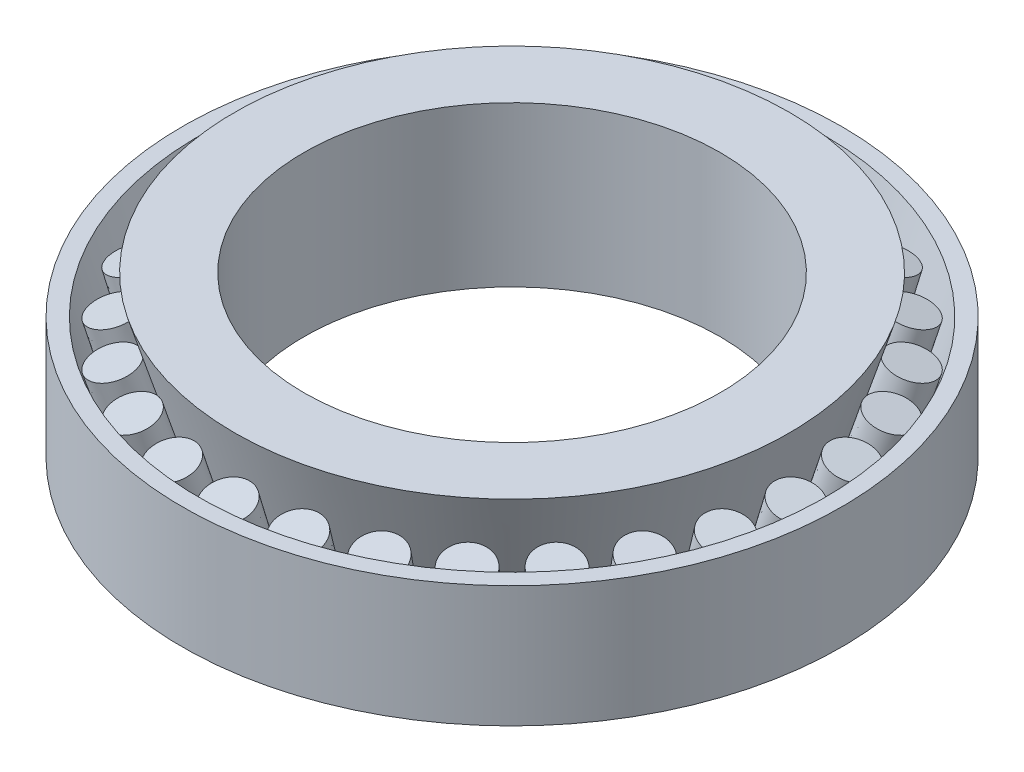
SolidWorks part; units mm, degrees
material "1023 Tôle d'acier au carbone (SS)"
ref_plane "Plan de face" through (0, 0, 0) normal (0, 0, 1) x (1, 0, 0)
ref_plane "Plan de dessus" through (0, 0, 0) normal (0, 1, 0) x (1, 0, 0)
ref_plane "Plan de droite" through (0, 0, 0) normal (1, 0, 0) x (0, 0, -1)
sketch "Esquisse5" plane through (0, 0, 0) normal (0, 0, 1) x (1, 0, 0)
  line L0 (0, 0) -> (0, 38.3619) construction
  line L1 (-30, 0) -> (-33, 0)
  line L2 (-33, 0) -> (-40, 23)
  line L3 (-40, 23) -> (-30, 23)
  line L4 (-30, 23) -> (-30, 0)
  line L5 (-47.5, 17.5) -> (-47.5, 0)
  line L6 (-47.5, 0) -> (-40, 0)
  line L7 (-40, 0) -> (-45.1193, 17.5)
  line L8 (-45.1193, 17.5) -> (-47.5, 17.5)
  line L9 (-42.5596, 8.75) -> (0, 21.2) construction
  dimension "D1" = 60
  dimension "D2" = 95
  dimension "D3" = 23
  dimension "D4" = 17.5
  dimension "D5" = 66
  dimension "D6" = 80
  dimension "D7" = 23
  dimension "D8" = 1.8
  dimension "D9" = 80
revolve "Révolution1" add sketch "Esquisse5" angle 360 about L0
sketch "Esquisse6" plane through (0, 0, 0) normal (0, 0, 1) x (1, 0, 0)
  line L0 (-41.7227, 17.5) -> (-36.5, 0) construction
  line L1 (-40.9782, 15.0053) -> (-37.8509, 15.9386)
  line L2 (-40, 23) -> (-33, 0) construction
  line L3 (-37.8509, 15.9386) -> (-33.6675, 2.1932)
  line L4 (-33.6675, 2.1932) -> (-36.8694, 1.2376)
  line L5 (-40.9782, 15.0053) -> (-36.8694, 1.2376)
  line L6 (-45.1193, 17.5) -> (-38.3261, 17.5) construction
  line L7 (47.5, 17.5) -> (-47.5, 17.5) construction
  line L8 (-40, 0) -> (-33, 0) construction
revolve "Révolution2" add sketch "Esquisse6" angle 360 about L0
pattern_circular "Répétition circulaire1" count 28 over 360 about axis through (0, 0, 0) along (0, 1, 0) of "Révolution2"
